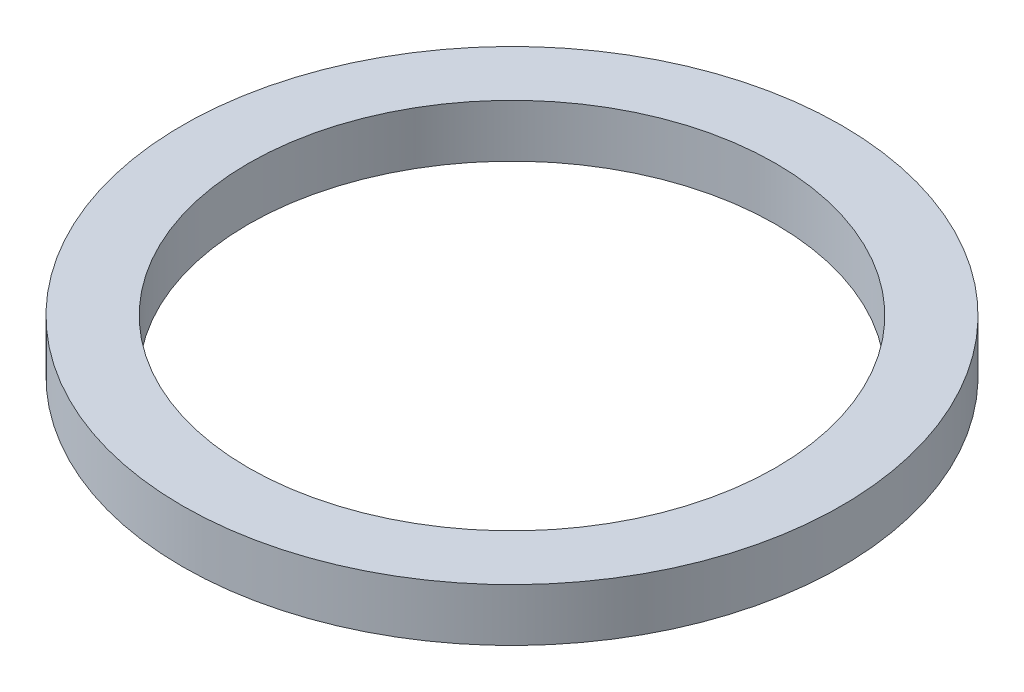
SolidWorks part; units mm, degrees
ref_plane "Plan de face" through (0, 0, 0) normal (0, 0, 1) x (1, 0, 0)
ref_plane "Plan de dessus" through (0, 0, 0) normal (0, 1, 0) x (1, 0, 0)
ref_plane "Plan de droite" through (0, 0, 0) normal (1, 0, 0) x (0, 0, -1)
sketch "Esquisse1" plane through (0, 0, 0) normal (0, 1, 0) x (1, 0, 0)
  circle A0 centre (0, 0) radius 18.75
  circle A1 centre (0, 0) radius 15
extrude "Boss.-Extru.1" add sketch "Esquisse1" along normal blind 3
